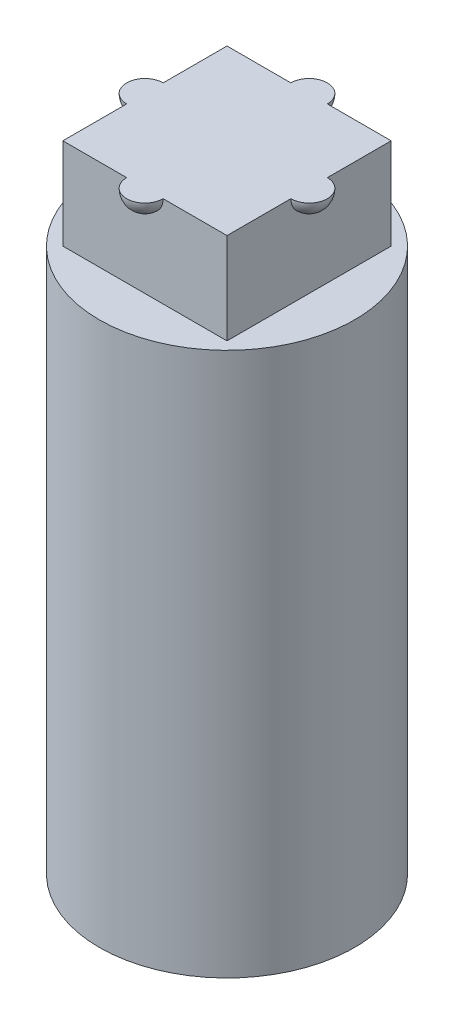
SolidWorks part; units mm, degrees
ref_plane "前视基准面" through (0, 0, 0) normal (0, 0, 1) x (1, 0, 0)
ref_plane "上视基准面" through (0, 0, 0) normal (0, 1, 0) x (1, 0, 0)
ref_plane "右视基准面" through (0, 0, 0) normal (1, 0, 0) x (0, 0, -1)
sketch "草图1" plane through (0, 0, 0) normal (0, 1, 0) x (1, 0, 0)
  line L1 (-0.95, 1.2) -> (0.95, 1.2)
  line L2 (-1.2, 0.95) -> (-1.2, -0.95)
  line L3 (-0.95, -1.2) -> (0.95, -1.2)
  line L4 (1.2, 0.95) -> (1.2, -0.95)
  circle A0 centre (0, 0) radius 3.5
  arc A1 (0.95, -1.2) -> (1.2, -0.95) centre (1.2, -1.2) ccw
  arc A2 (-1.2, -0.95) -> (-0.95, -1.2) centre (-1.2, -1.2) ccw
  arc A3 (-0.95, 1.2) -> (-1.2, 0.95) centre (-1.2, 1.2) ccw
  arc A4 (1.2, 0.95) -> (0.95, 1.2) centre (1.2, 1.2) ccw
  point P0 (0, 0)
  dimension "D3" = 7
  dimension "D4" = 0.5
  dimension "D5" = 0.5
  dimension "D6" = 0.5
  dimension "D7" = 0.5
  dimension "D1" = 2.4
  dimension "D2" = 2.4
extrude "凸台-拉伸1" add sketch "草图1" along normal blind 4
sketch "草图2" plane through (0, 4, 0) normal (0, 1, 0) x (1, 0, 0)
  circle A0 centre (0, 0) radius 3.5
  dimension "D1" = 7
extrude "凸台-拉伸2" add sketch "草图2" along normal blind 10.9
sketch "草图3" plane through (0, 14.9, 0) normal (0, 1, 0) x (1, 0, 0)
  line L1 (-2.25, 2.25) -> (2.25, 2.25)
  line L2 (-2.25, 2.25) -> (-2.25, -2.25)
  line L3 (-2.25, -2.25) -> (2.25, -2.25)
  line L4 (2.25, 2.25) -> (2.25, -2.25)
  line L5 (-2.25, 2.25) -> (2.25, -2.25) construction
  line L6 (-2.25, -2.25) -> (2.25, 2.25) construction
  point P0 (0, 0)
  dimension "D1" = 4.5
  dimension "D2" = 4.5
extrude "凸台-拉伸3" add sketch "草图3" along normal blind 2.5
sketch "草图4" plane through (0, 17.4, 0) normal (0, 1, 0) x (1, 0, 0)
  line L0 (2.25, 2.25) -> (-2.25, 2.25) construction
  line L1 (-2.25, -2.25) -> (2.25, -2.25) construction
  line L2 (0, 2.75) -> (0, 1.75)
  line L3 (0, -1.75) -> (0, -2.75)
  arc A0 (0, 2.75) -> (0, 1.75) centre (0, 2.25) ccw
  arc A1 (0, -1.75) -> (0, -2.75) centre (0, -2.25) ccw
  dimension "D1" = 1
  dimension "D2" = 1
revolve "旋转1" add sketch "草图4" angle 360 about L2
sketch "草图5" plane through (0, 17.4, 0) normal (0, 1, 0) x (1, 0, 0)
  line L0 (-2.25, 2.25) -> (-2.25, -2.25) construction
  line L1 (2.25, -2.25) -> (2.25, 2.25) construction
  line L2 (-2.75, 0) -> (-1.75, 0)
  line L3 (1.75, 0) -> (2.75, 0)
  arc A0 (-1.75, 0) -> (-2.75, 0) centre (-2.25, 0) ccw
  arc A1 (2.75, 0) -> (1.75, 0) centre (2.25, 0) ccw
  dimension "D1" = 1
  dimension "D2" = 1
revolve "旋转2" add sketch "草图5" angle 360 about L2
sketch "草图6" plane through (0, 17.4, 0) normal (0, 1, 0) x (1, 0, 0)
  circle A0 centre (0, 0) radius 3.25
extrude "切除-拉伸1" cut sketch "草图6" along normal blind 2.5
